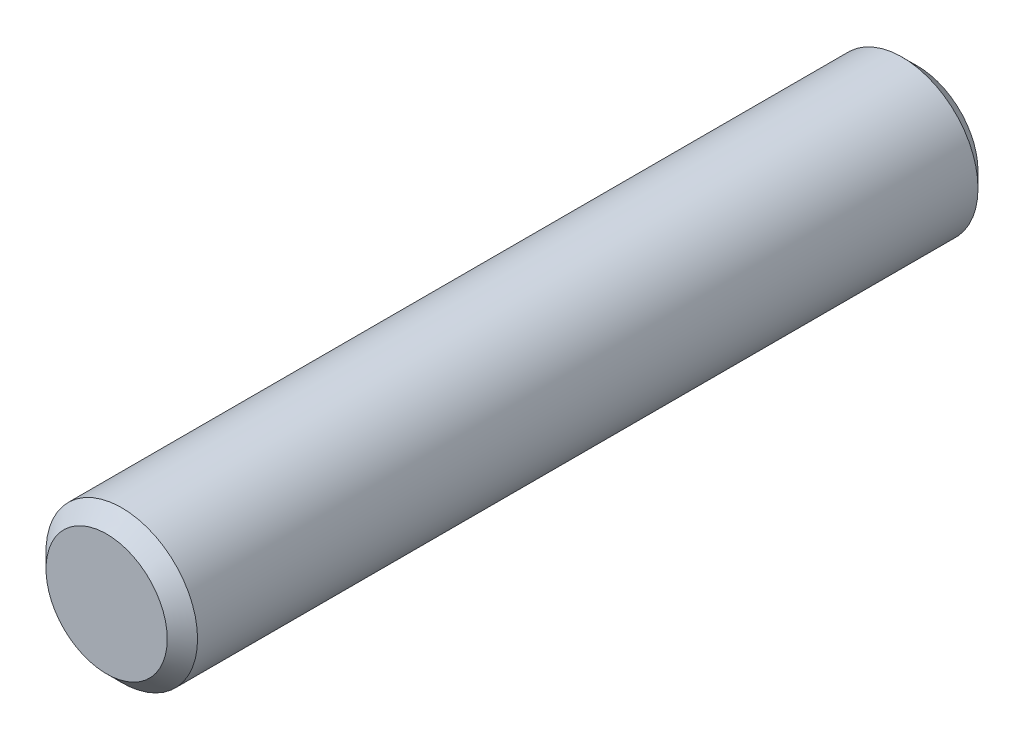
SolidWorks part; units mm, degrees
material "Plain Carbon Steel"
ref_plane "Front" through (0, 0, 0) normal (0, 0, 1) x (1, 0, 0)
ref_plane "Top" through (0, 0, 0) normal (0, 1, 0) x (1, 0, 0)
ref_plane "Right" through (0, 0, 0) normal (1, 0, 0) x (0, 0, -1)
sketch "Sketch1" plane through (0, 0, 0) normal (0, 0, 1) x (1, 0, 0)
  circle A0 centre (0, 0) radius 7.9375
  dimension "Diameter" = 15.875
sketch "Sketch2" plane through (0, 0, 0) normal (1, 0, 0) x (0, 0, -1)
  line L0 (-42.4625, 0) -> (42.4625, 0) construction
  line L1 (8.3375, 7.9375) -> (8.3375, -7.9375) construction
  line L2 (8.7312, 0) -> (-8.7312, 0) construction
  line L3 (-8.3375, 7.9375) -> (-8.3375, -7.9375) construction
  line L4 (-42.4625, 7.9375) -> (-42.4625, -7.9375) construction
  line L5 (42.4625, 7.9375) -> (42.4625, -7.9375) construction
  point P3 (8.3375, 0)
  point P8 (0, 0)
  point P9 (-8.3375, 0)
  point P15 (-42.4625, 0)
  point P18 (42.4625, 0)
  dimension "D1" = 15.875
  dimension "Length" = 84.925
  dimension "D2" = 50.8
  dimension "D3" = 50.8
sketch "Sketch3" plane through (0, 0, 0) normal (0, 0, 1) x (1, 0, 0)
  circle A0 centre (0, 0) radius 7.9375
  dimension "D1" = 15.875
extrude "Boss-Extrude1" add sketch "Sketch3" along normal mid plane 84.925
chamfer "Chamfer1" distance 1.5875 angle 45 2 edges at (7.9375, 0, -42.4625) (7.9375, 0, 42.4625)
equation "\"D1@Sketch3\" = \"Diameter@Sketch1\""
equation "\"D1@Boss-Extrude1\" = \"Length@Sketch2\""
equation "\"D1@Chamfer1\" = \"Diameter@Sketch1\" * .1"
equation "\"D1@Sketch2\" = \"Diameter@Sketch1\""
